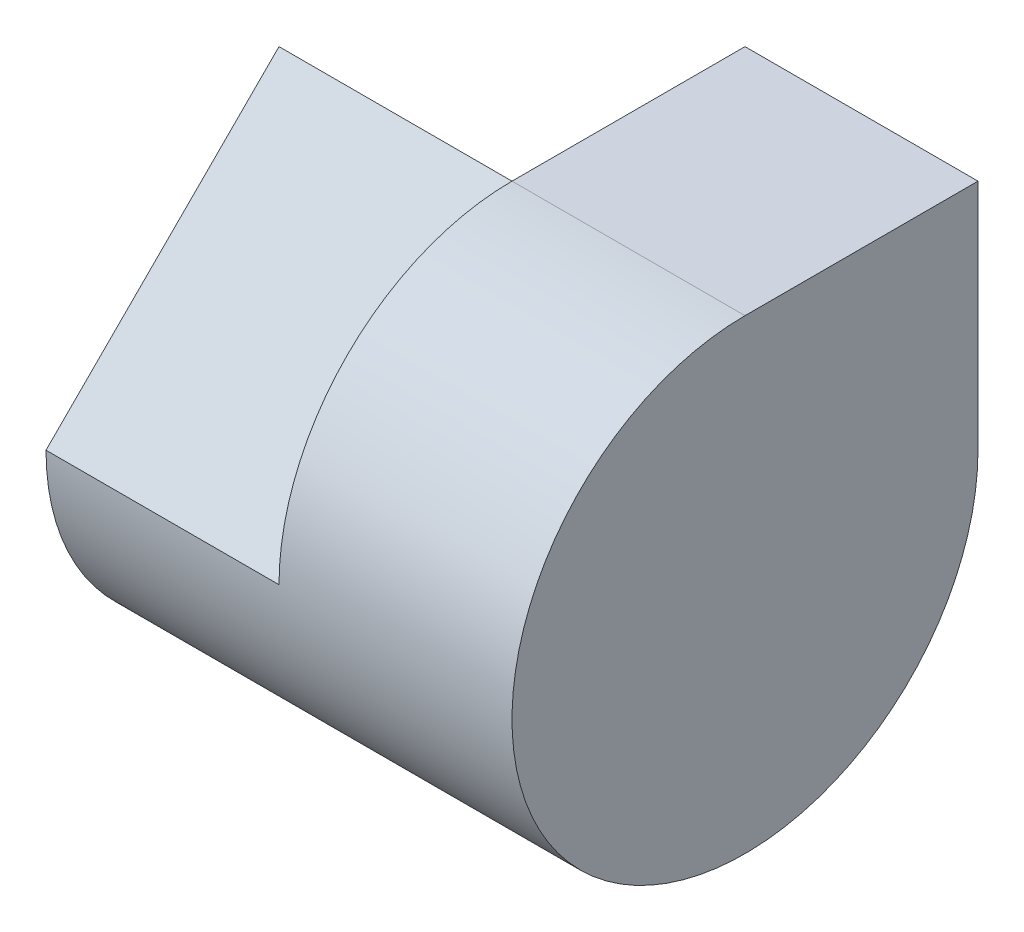
SolidWorks part; units mm, degrees
ref_plane "Front" through (0, 0, 0) normal (0, 0, 1) x (1, 0, 0)
ref_plane "Top" through (0, 0, 0) normal (0, 1, 0) x (1, 0, 0)
ref_plane "Right" through (0, 0, 0) normal (1, 0, 0) x (0, 0, -1)
sketch "Sketch1" plane through (0, 0, 0) normal (0, 1, 0) x (1, 0, 0)
  line L1 (-2, -2) -> (2, -2)
  line L2 (-2, -2) -> (-2, 2)
  line L3 (-2, 2) -> (2, 2)
  line L4 (2, -2) -> (2, 2)
  line L5 (-2, -2) -> (2, 2) construction
  line L6 (-2, 2) -> (2, -2) construction
  point P0 (0, 0)
  dimension "D1" = 4
  dimension "D2" = 4
extrude "Boss-Extrude1" add sketch "Sketch1" along normal blind 4
sketch "Sketch2" plane through (-2, 0, 0) normal (-1, 0, 0) x (0, 0, 1)
  line L0 (2, 2) -> (0, 4)
  line L1 (2, 4) -> (2, 0) construction
  line L2 (-2, 4) -> (2, 4) construction
  line L4 (-2, 4) -> (-2, 0) construction
  line L5 (0, 4) -> (0, 2)
  line L6 (0, 2) -> (-2, 2)
  line L9 (-2, 0) -> (2, 0)
  line L10 (2, 0) -> (2, 4)
  line L11 (2, 4) -> (-2, 4)
  line L12 (-2, 4) -> (-2, 0)
  line L13 (-2, 0) -> (2, 0)
  line L14 (2, 0) -> (2, 4)
  line L15 (2, 4) -> (-2, 4)
  line L16 (-2, 4) -> (-2, 0)
  dimension "D1" = 0
extrude "Cut-Extrude1" cut sketch "Sketch2" against normal blind 2
sketch "Sketch3" plane through (0, 0, 0) normal (-1, 0, 0) x (0, 0, 1)
  line L3 (0, 4) -> (2, 2)
  line L4 (2, 2) -> (2, 4)
  line L5 (2, 4) -> (0, 4)
  line L6 (0, 4) -> (2, 2)
  line L7 (2, 2) -> (2, 4)
  line L8 (2, 4) -> (0, 4)
  line L12 (2, 2) -> (0, 4)
  line L13 (0, 4) -> (0, 2)
  line L14 (0, 2) -> (-2, 2)
  line L15 (-2, 2) -> (-2, 0)
  line L16 (-2, 0) -> (2, 0)
  line L17 (2, 0) -> (2, 2)
  line L18 (2, 2) -> (0, 4)
  line L19 (0, 4) -> (0, 2)
  line L20 (0, 2) -> (-2, 2)
  line L21 (-2, 2) -> (-2, 0)
  line L22 (-2, 0) -> (2, 0)
  line L23 (2, 0) -> (2, 2)
  arc A0 (0, 4) -> (-2, 2) centre (0, 2) cw
  line M11 (2, 2) -> (2, 4)
  line M12 (2, 4) -> (0, 4)
  dimension "D1" = 0
  dimension "D2" = 0
extrude "Cut-Extrude2" cut sketch "Sketch3" against normal mid plane 40 contours A0 M12 M11 | L23 A0 L22 | L22 A0 L21
